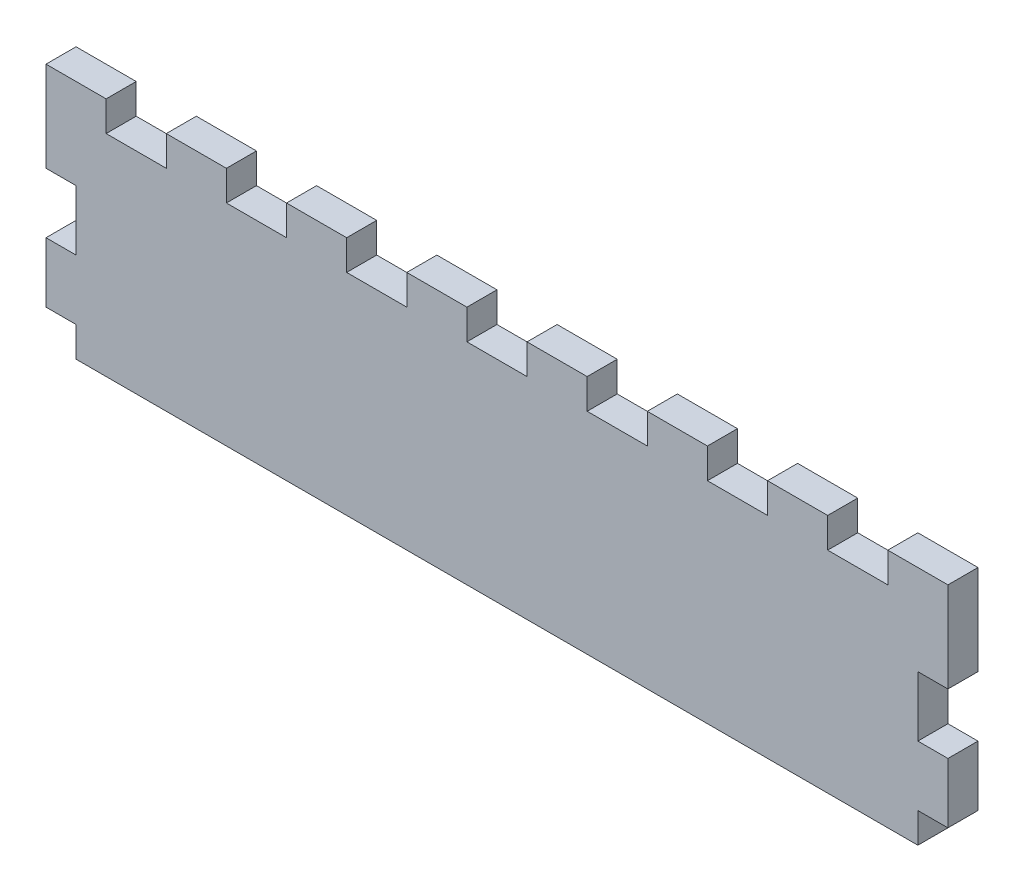
SolidWorks part; units mm, degrees
ref_plane "Front Plane" through (0, 0, 0) normal (0, 0, 1) x (1, 0, 0)
ref_plane "Top Plane" through (0, 0, 0) normal (0, 1, 0) x (1, 0, 0)
ref_plane "Right Plane" through (0, 0, 0) normal (1, 0, 0) x (0, 0, -1)
sketch "Sketch1" plane through (0, 0, 0) normal (0, 0, 1) x (1, 0, 0)
  line L1 (-95.25, -25.4) -> (95.25, -25.4)
  line L2 (-95.25, -25.4) -> (-95.25, 25.4)
  line L3 (-95.25, 25.4) -> (95.25, 25.4)
  line L4 (95.25, -25.4) -> (95.25, 25.4)
  line L5 (-95.25, -25.4) -> (95.25, 25.4) construction
  line L6 (-95.25, 25.4) -> (95.25, -25.4) construction
  point P0 (0, 0)
  dimension "D1" = 50.8
  dimension "D2" = 190.5
extrude "Boss-Extrude1" add sketch "Sketch1" along normal blind 6.35
sketch "Sketch2" plane through (0, 0, 6.35) normal (0, 0, 1) x (1, 0, 0)
  line L0 (-95.25, 25.4) -> (-95.25, -25.4) construction
  line L1 (-95.25, -6.35) -> (-88.9, -6.35)
  line L2 (-95.25, -6.35) -> (-95.25, 6.35)
  line L3 (-95.25, 6.35) -> (-88.9, 6.35)
  line L4 (-88.9, -6.35) -> (-88.9, 6.35)
  dimension "D1" = 6.35
  dimension "D2" = 12.7
  dimension "D3" = 19.05
extrude "Cut-Extrude1" cut sketch "Sketch2" against normal through all
sketch "Sketch3" plane through (0, 0, 6.35) normal (0, 0, 1) x (1, 0, 0)
  line L1 (-95.25, -25.4) -> (-88.9, -25.4)
  line L2 (-95.25, -25.4) -> (-95.25, -19.05)
  line L3 (-95.25, -19.05) -> (-88.9, -19.05)
  line L4 (-88.9, -25.4) -> (-88.9, -19.05)
  dimension "D1" = 6.35
  dimension "D2" = 6.35
extrude "Cut-Extrude2" cut sketch "Sketch3" against normal through all
mirror "Mirror1" about plane through (0, 0, 0) normal (1, 0, 0) of "Cut-Extrude2"
mirror "Mirror2" about plane through (0, 0, 0) normal (1, 0, 0) of "Cut-Extrude1"
sketch "Sketch4" plane through (0, 0, 6.35) normal (0, 0, 1) x (1, 0, 0)
  line L0 (95.25, 25.4) -> (-95.25, 25.4) construction
  line L1 (-82.55, 25.4) -> (-69.85, 25.4)
  line L2 (-82.55, 25.4) -> (-82.55, 19.05)
  line L3 (-82.55, 19.05) -> (-69.85, 19.05)
  line L4 (-69.85, 25.4) -> (-69.85, 19.05)
  dimension "D1" = 12.7
  dimension "D2" = 6.35
  dimension "D3" = 12.7
extrude "Cut-Extrude3" cut sketch "Sketch4" against normal through all
pattern_linear "LPattern1" count 7 spacing 25.4 along (1, 0, 0) of "Cut-Extrude3"
